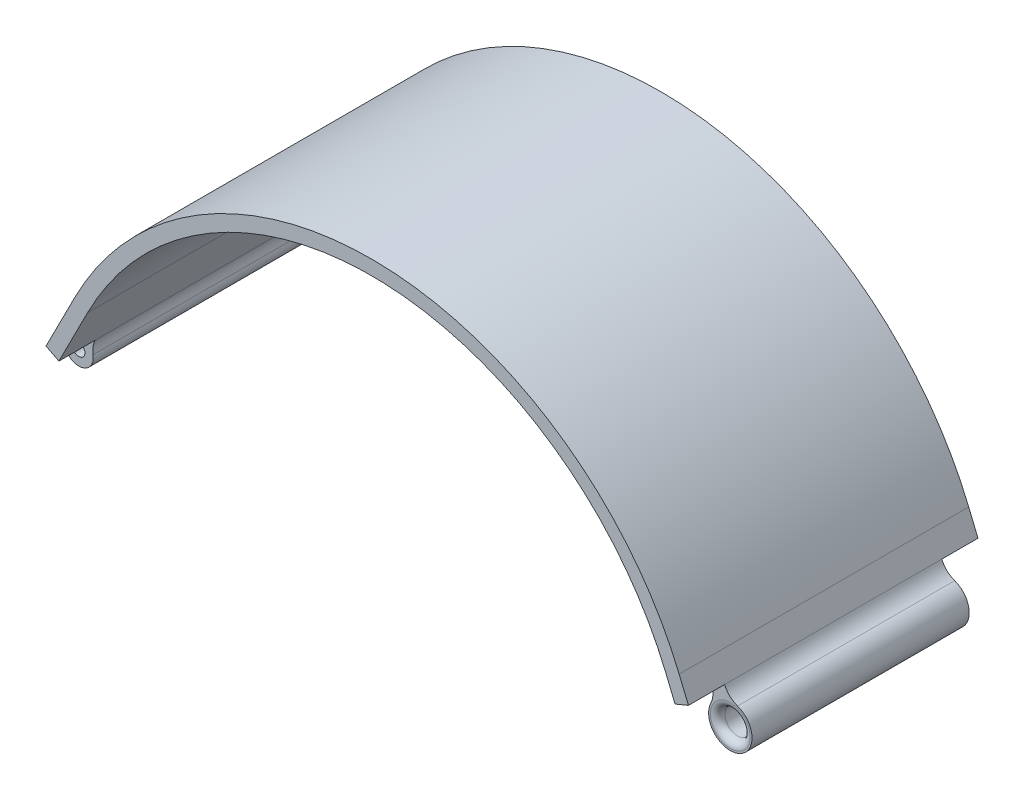
SolidWorks part; units mm, degrees
material "ABS"
ref_plane "Front" through (0, 0, 0) normal (0, 0, 1) x (1, 0, 0)
ref_plane "Top" through (0, 0, 0) normal (0, 1, 0) x (1, 0, 0)
ref_plane "Right" through (0, 0, 0) normal (1, 0, 0) x (0, 0, -1)
sketch "Croquis1" plane through (0, 0, 0) normal (0, 0, 1) x (1, 0, 0)
  line L0 (-78.4193, 20.002) -> (-87.4943, 2.1795)
  line L1 (81.3196, 13.7039) -> (85.1415, 4.4631)
  line L2 (-81.9838, 21.817) -> (-91.0588, 3.9945)
  line L3 (85.016, 15.2327) -> (88.8378, 5.9918)
  arc A0 (-78.4193, 20.002) -> (81.3196, 13.7039) centre (0, -19.9281) cw
  arc A1 (-81.9838, 21.817) -> (85.016, 15.2327) centre (0, -19.9281) cw
  arc A2 (-91.0588, 3.9945) -> (-87.4943, 2.1795) centre (-90.8484, 0) ccw
  arc A3 (85.1415, 4.4631) -> (88.8378, 5.9918) centre (89.1516, 0) ccw
  arc A8 (-78.4193, 20.002) -> (81.3196, 13.7039) centre (0, -19.9281) cw construction
  circle A10 centre (-90.8484, 0) radius 1.7
  circle A11 centre (89.1516, 0) radius 3.5
  dimension "D3" = 88
  dimension "D10" = 4
  dimension "D11" = 3.4
  dimension "D4" = 6
  dimension "D5" = 7
  dimension "D6" = 180
  dimension "D7" = 20
  dimension "D9" = 10
  dimension "D2" = 4
extrude "Saliente-Extruir1" add sketch "Croquis1" along normal mid plane 80
fillet "Redondeo1" radius 6 4 edges at (85.1415, 4.4631, 0) (88.8378, 5.9918, 0) (-91.0588, 3.9945, 0) (-87.4943, 2.1795, 0)
sketch "Croquis2" plane through (0, 0, -40) normal (0, 0, -1) x (-1, 0, 0)
  line L0 (89.9082, 6.2543) -> (86.3436, 4.4393)
  line L1 (-87.5814, 9.0296) -> (-83.8851, 7.5009)
  line L4 (78.4193, 20.002) -> (86.3436, 4.4393)
  line L5 (89.9082, 6.2543) -> (81.9838, 21.817)
  line L6 (-85.016, 15.2327) -> (-87.5814, 9.0296)
  line L7 (-83.8851, 7.5009) -> (-81.3196, 13.7039)
  arc A10 (78.4193, 20.002) -> (-81.3196, 13.7039) centre (0, -19.9281) ccw
  arc A11 (86.9078, 0.6867) -> (86.3436, 4.4393) centre (80.9969, 1.7168) ccw
  arc A12 (86.9078, 0.6867) -> (92.611, 3.5907) centre (90.8484, 0) ccw
  arc A13 (89.9082, 6.2543) -> (92.611, 3.5907) centre (95.2549, 8.9768) ccw
  arc A14 (81.9838, 21.817) -> (-85.016, 15.2327) centre (0, -19.9281) ccw
  arc A15 (-91.1388, 5.6614) -> (-87.5814, 9.0296) centre (-93.1259, 11.3227) ccw
  arc A16 (-91.1388, 5.6614) -> (-83.7461, 2.6039) centre (-89.1516, 0) ccw
  arc A17 (-83.8851, 7.5009) -> (-83.7461, 2.6039) centre (-78.3406, 5.2078) ccw
  arc A21 (86.9078, 0.6867) -> (86.3436, 4.4393) centre (80.9969, 1.7168) ccw
  arc A22 (86.9078, 0.6867) -> (92.611, 3.5907) centre (90.8484, 0) ccw
  arc A23 (89.9082, 6.2543) -> (92.611, 3.5907) centre (95.2549, 8.9768) ccw
  arc A25 (-91.1388, 5.6614) -> (-87.5814, 9.0296) centre (-93.1259, 11.3227) ccw
  arc A26 (-91.1388, 5.6614) -> (-83.7461, 2.6039) centre (-89.1516, 0) ccw
  arc A27 (-83.8851, 7.5009) -> (-83.7461, 2.6039) centre (-78.3406, 5.2078) ccw
  dimension "D1" = 0
extrude "Cortar-Extruir1" cut sketch "Croquis2" against normal blind 10
mirror "Simetría1" about plane through (0, 0, 0) normal (0, 0, 1) of "Cortar-Extruir1"
fillet "Redondeo2" radius 2 2 edges at (85.6516, 0, -30) (92.6516, 0, 30)
